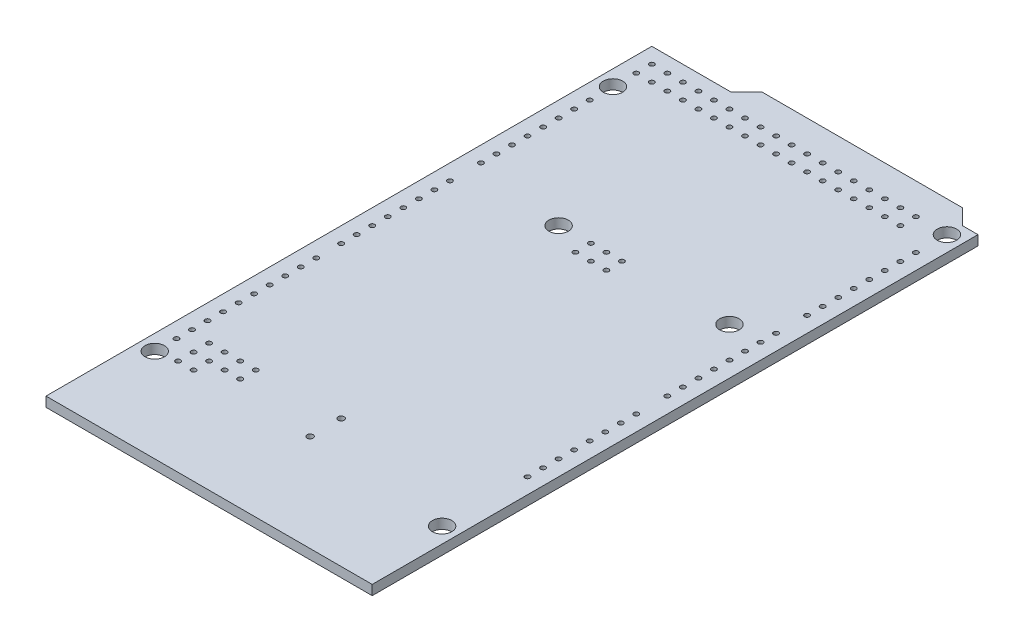
SolidWorks part; units mm, degrees
material "E-Glass Fiber"
ref_plane "Front Plane" through (0, 0, 0) normal (0, 0, 1) x (1, 0, 0)
ref_plane "Top Plane" through (0, 0, 0) normal (0, 1, 0) x (1, 0, 0)
ref_plane "Right Plane" through (0, 0, 0) normal (1, 0, 0) x (0, 0, -1)
sketch "Sketch1" plane through (0, 0, 0) normal (0, 1, 0) x (1, 0, 0)
  line L0 (-55, 0) -> (55, 0) construction
  line L1 (0, 0) -> (-53.34, 0)
  line L2 (0, 0) -> (0, 99.06)
  line L3 (-5.08, 101.6) -> (-37.846, 101.6)
  line L4 (-53.34, 0) -> (-53.34, 99.06)
  line L5 (-53.34, 99.06) -> (-40.386, 99.06)
  line L6 (-40.386, 99.06) -> (-37.846, 101.6)
  line L7 (-5.08, 101.6) -> (-2.54, 99.06)
  line L8 (-2.54, 99.06) -> (0, 99.06)
  circle A0 centre (-7.62, 66.04) radius 1.5875
  circle A1 centre (-35.56, 66.04) radius 1.5875
  circle A2 centre (-2.54, 13.97) radius 1.5875
  circle A3 centre (-50.8, 15.24) radius 1.5875
  circle A4 centre (-2.54, 96.52) radius 1.5875
  circle A5 centre (-50.8, 90.17) radius 1.5875
  dimension "D8" = 3.175
  dimension "D16" = 96.52
  dimension "D1" = 101.6
  dimension "D2" = 53.34
  dimension "D3" = 99.06
  dimension "D4" = 2.54
  dimension "D5" = 45
  dimension "D6" = 45
  dimension "D7" = 40.386
  dimension "D9" = 66.04
  dimension "D10" = 35.56
  dimension "D11" = 7.62
  dimension "D12" = 13.97
  dimension "D13" = 2.54
  dimension "D14" = 15.24
  dimension "D15" = 50.8
  dimension "D17" = 90.17
extrude "Boss-Extrude1" add sketch "Sketch1" against normal blind 1.6
sketch "Sketch2" plane through (0, 0, 0) normal (0, 1, 0) x (1, 0, 0)
  line L0 (0, -0.9075) -> (0, 0.9075) construction
  line L1 (-0.9075, 0) -> (0.9075, 0) construction
  circle A0 centre (-2.54, 27.94) radius 0.4
  dimension "D1" = 0.8
  dimension "D2" = 2.54
  dimension "D3" = 27.94
extrude "Cut-Extrude1" cut sketch "Sketch2" against normal blind 1.65
sketch "Sketch3" plane through (0, 0, 0) normal (0, 1, 0) x (1, 0, 0)
  line L0 (0, -0.9075) -> (0, 0.9075) construction
  line L1 (-0.9075, 0) -> (0.9075, 0) construction
  circle A0 centre (-50.8, 18.796) radius 0.4
  dimension "D2" = 0.8
  dimension "D1" = 50.8
  dimension "D3" = 18.796
extrude "Cut-Extrude2" cut sketch "Sketch3" against normal blind 1.65
pattern_linear "LPattern1" count 26 spacing 2.54 along (0, 0, -1) skipping (8, 0), (17, 0) of "Cut-Extrude1"
sketch "Sketch4" plane through (0, 0, 0) normal (0, 1, 0) x (1, 0, 0)
  line L0 (-0.9075, 0) -> (0.9075, 0) construction
  line L1 (0, -0.9075) -> (0, 0.9075) construction
  circle A0 centre (-50.8, 45.72) radius 0.4
  dimension "D3" = 0.8
  dimension "D1" = 45.72
  dimension "D2" = 50.8
extrude "Cut-Extrude3" cut sketch "Sketch4" against normal blind 1.65
pattern_linear "LPattern2" count 10 spacing 2.54 along (0, 0, -1) of "Cut-Extrude2"
pattern_linear "LPattern3" count 17 spacing 2.54 along (0, 0, -1) skipping (8, 0) of "Cut-Extrude3"
sketch "Sketch5" plane through (0, 0, 0) normal (0, 1, 0) x (1, 0, 0)
  line L0 (-27.89, 66.18) -> (-27.89, 63.64) construction
  line L1 (-30.43, 66.18) -> (-25.35, 66.18) construction
  line L2 (-30.43, 66.18) -> (-30.43, 63.64) construction
  line L3 (-30.43, 63.64) -> (-25.35, 63.64) construction
  line L4 (-25.35, 66.18) -> (-25.35, 63.64) construction
  line L5 (-0.9075, 0) -> (0.9075, 0) construction
  line L6 (0, -0.9075) -> (0, 0.9075) construction
  circle A0 centre (-30.43, 66.18) radius 0.4
  circle A1 centre (-27.89, 66.18) radius 0.4
  circle A2 centre (-25.35, 66.18) radius 0.4
  circle A3 centre (-25.35, 63.64) radius 0.4
  circle A4 centre (-27.89, 63.64) radius 0.4
  circle A5 centre (-30.43, 63.64) radius 0.4
  circle A6 centre (-47.498, 15.748) radius 0.4
  circle A7 centre (-47.498, 18.288) radius 0.4
  circle A8 centre (-47.498, 20.828) radius 0.4
  circle A9 centre (-44.958, 20.828) radius 0.4
  circle A10 centre (-44.958, 18.288) radius 0.4
  circle A11 centre (-44.958, 15.748) radius 0.4
  circle A12 centre (-42.418, 18.288) radius 0.4
  circle A13 centre (-42.418, 20.828) radius 0.4
  circle A14 centre (-39.878, 20.828) radius 0.4
  circle A15 centre (-39.878, 18.288) radius 0.4
  circle A16 centre (-26.035, 20.955) radius 0.5
  circle A17 centre (-26.035, 15.875) radius 0.5
  dimension "D4" = 0.8
  dimension "D14" = 1
  dimension "D1" = 2.54
  dimension "D2" = 2.54
  dimension "D3" = 2.54
  dimension "D5" = 63.64
  dimension "D6" = 30.43
  dimension "D7" = 2.54
  dimension "D8" = 2.54
  dimension "D9" = 2.54
  dimension "D10" = 2.54
  dimension "D11" = 2.54
  dimension "D12" = 47.498
  dimension "D13" = 15.748
  dimension "D15" = 5.08
  dimension "D16" = 15.875
  dimension "D17" = 26.035
extrude "Cut-Extrude4" cut sketch "Sketch5" against normal blind 10
sketch "Sketch6" plane through (0, 0, 0) normal (0, 1, 0) x (1, 0, 0)
  line L0 (0, -55) -> (0, 55) construction
  line L1 (-55, 0) -> (55, 0) construction
  line L2 (-20.193, 29.845) -> (-20.193, 32.385) construction
  circle A0 centre (-20.193, 29.845) radius 0.4
  circle A1 centre (-12.573, 29.845) radius 0.4
  circle A2 centre (-20.193, 32.385) radius 0.4
  circle A3 centre (-12.573, 32.385) radius 0.4
  circle A4 centre (-20.193, 34.925) radius 0.4
  circle A5 centre (-12.573, 34.925) radius 0.4
  circle A6 centre (-20.193, 37.465) radius 0.4
  circle A7 centre (-12.573, 37.465) radius 0.4
  circle A8 centre (-20.193, 40.005) radius 0.4
  circle A9 centre (-12.573, 40.005) radius 0.4
  circle A10 centre (-20.193, 42.545) radius 0.4
  circle A11 centre (-12.573, 42.545) radius 0.4
  circle A12 centre (-20.193, 45.085) radius 0.4
  circle A13 centre (-12.573, 45.085) radius 0.4
  circle A14 centre (-20.193, 47.625) radius 0.4
  circle A15 centre (-12.573, 47.625) radius 0.4
  circle A16 centre (-20.193, 50.165) radius 0.4
  circle A17 centre (-12.573, 50.165) radius 0.4
  circle A18 centre (-20.193, 52.705) radius 0.4
  circle A19 centre (-12.573, 52.705) radius 0.4
  circle A20 centre (-20.193, 55.245) radius 0.4
  circle A21 centre (-12.573, 55.245) radius 0.4
  circle A22 centre (-20.193, 57.785) radius 0.4
  circle A23 centre (-12.573, 57.785) radius 0.4
  circle A24 centre (-20.193, 60.325) radius 0.4
  circle A25 centre (-12.573, 60.325) radius 0.4
  circle A26 centre (-20.193, 62.865) radius 0.4
  circle A27 centre (-12.573, 62.865) radius 0.4
  dimension "D1" = 0.8
  dimension "D2" = 7.62
  dimension "D3" = 12.573
  dimension "D4" = 29.845
  dimension "D6" = 2.54
  dimension "D5" = 14
extrude "Cut-Extrude5" [suppressed] cut sketch "Sketch6" against normal blind 10
sketch "Sketch7" plane through (0, 0, 0) normal (0, 1, 0) x (1, 0, 0)
  line L0 (-55, 0) -> (55, 0) construction
  line L1 (0, -55) -> (0, 55) construction
  circle A0 centre (-50.8, 96.52) radius 0.4
  circle A1 centre (-50.8, 93.98) radius 0.4
  dimension "D1" = 0.8
  dimension "D2" = 2.54
  dimension "D3" = 96.52
  dimension "D4" = 50.8
extrude "Cut-Extrude6" cut sketch "Sketch7" against normal blind 10
pattern_linear "LPattern4" count 18 spacing 2.54 along (1, 0, 0) of "Cut-Extrude6"
equation "\"D13@Sketch5\"=0.001*25.4*620"
equation "\"D16@Sketch5\"=625*0.001*25.4"
equation "\"D17@Sketch5\"=1025*0.001*25.4"
